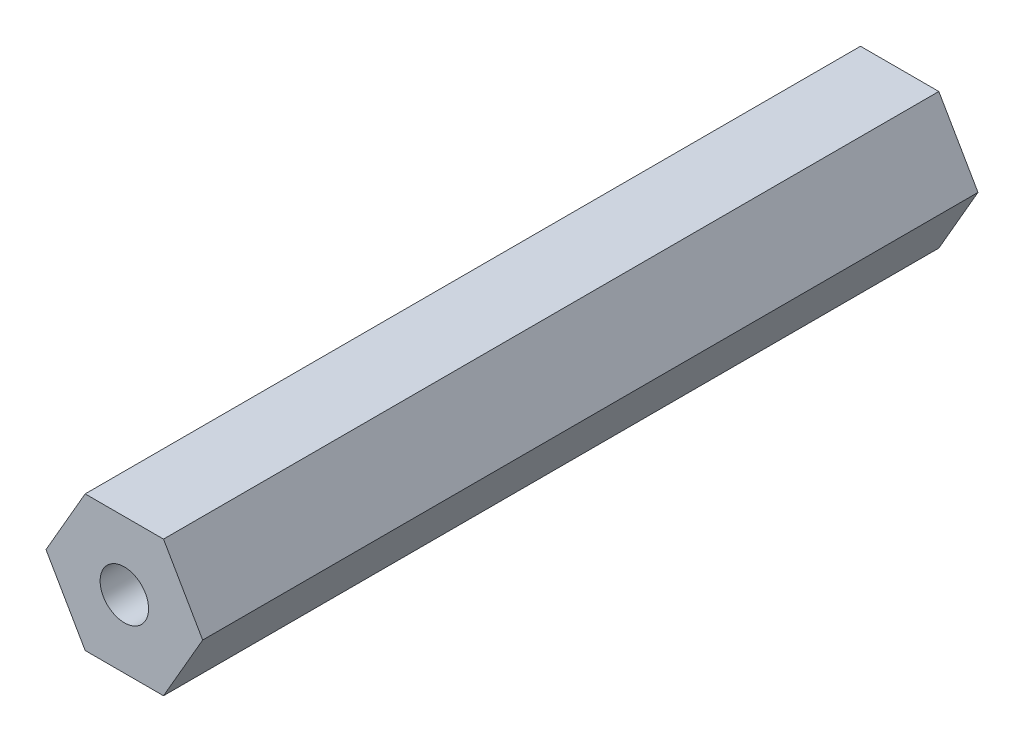
SolidWorks part; units mm, degrees
material "黃銅"
ref_plane "前基準面" through (0, 0, 0) normal (0, 0, 1) x (1, 0, 0)
ref_plane "上基準面" through (0, 0, 0) normal (0, 1, 0) x (1, 0, 0)
ref_plane "右基準面" through (0, 0, 0) normal (1, 0, 0) x (0, 0, -1)
sketch "草圖1" plane through (0, 0, 0) normal (0, 0, 1) x (1, 0, 0)
  line L1 (-2.0207, 3.5) -> (-4.0415, 0)
  line L2 (-4.0415, 0) -> (-2.0207, -3.5)
  line L3 (-2.0207, -3.5) -> (2.0207, -3.5)
  line L4 (2.0207, -3.5) -> (4.0415, 0)
  line L5 (4.0415, 0) -> (2.0207, 3.5)
  line L6 (2.0207, 3.5) -> (-2.0207, 3.5)
  circle A0 centre (0, 0) radius 3.5 construction
  dimension "D1" = 7
extrude "填料-伸長1" add sketch "草圖1" along normal blind 40
hole_wizard "M3x0.5 螺紋孔1" positions "草圖2" profile "草圖3" tap size "M3x0.5" standard "Ansi Metric" end condition through all
sketch "草圖2" plane through (0, 0, 40) normal (0, 0, 1) x (1, 0, 0)
  point P0 (0, 0)
sketch "草圖3" plane through (0, 0, 40) normal (1, 0, 0) x (0, -1, 0)
  line L0 (0, 0) -> (0, 40)
  line L1 (0, 40) -> (1.25, 40)
  line L2 (1.25, 40) -> (1.25, 0)
  line L5 (1.25, 0) -> (0, 0)
  line L11 (0, -6.35) -> (0, 107.95) construction
  dimension "貫穿螺孔鑽直徑" = 2.5
  dimension "貫穿螺孔鑽深度" = 40
